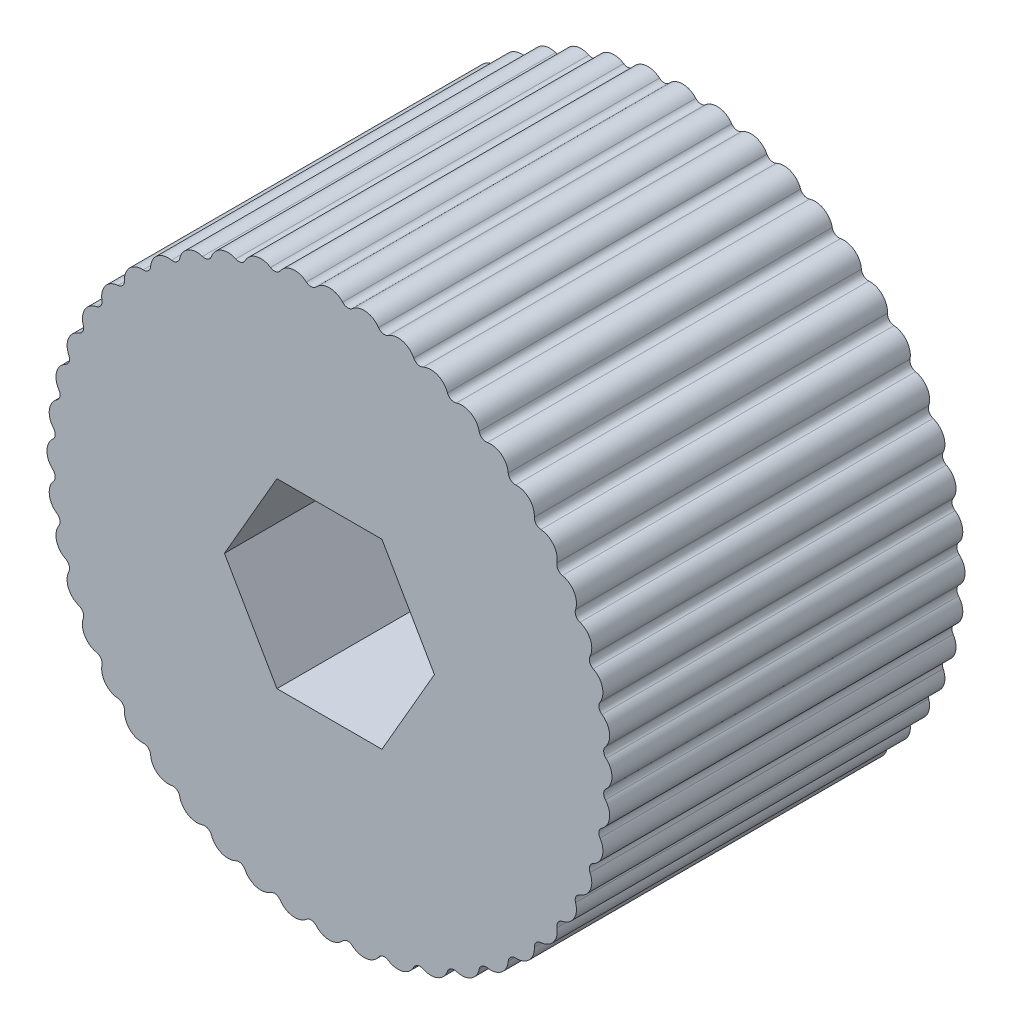
SolidWorks part; units mm, degrees
ref_plane "Front Plane" through (0, 0, 0) normal (0, 0, 1) x (1, 0, 0)
ref_plane "Top Plane" through (0, 0, 0) normal (0, 1, 0) x (1, 0, 0)
ref_plane "Right Plane" through (0, 0, 0) normal (1, 0, 0) x (0, 0, -1)
sketch "Sketch1" plane through (0, 0, 0) normal (0, 0, 1) x (1, 0, 0)
  line L1 (3.7762, 6.5405) -> (-3.7762, 6.5405)
  line L2 (-3.7762, 6.5405) -> (-7.5523, 0)
  line L3 (-7.5523, 0) -> (-3.7762, -6.5405)
  line L4 (-3.7762, -6.5405) -> (3.7762, -6.5405)
  line L5 (3.7762, -6.5405) -> (7.5523, 0)
  line L6 (7.5523, 0) -> (3.7762, 6.5405)
  circle A0 centre (0, 0) radius 6.5405 construction
  circle A1 centre (0, 0) radius 19.05
  dimension "D2" = 38.1
  dimension "D1" = 13.081
extrude "Boss-Extrude1" add sketch "Sketch1" along normal blind 25.4
sketch "Sketch2" plane through (0, 0, 25.4) normal (0, 0, 1) x (1, 0, 0)
  line L0 (19.0077, 1.2693) -> (19.0077, -1.2693)
  arc A0 (19.0077, 1.2693) -> (19.0077, -1.2693) centre (19.05, 0) cw
  circle A1 centre (0, 0) radius 19.05 construction
  dimension "D1" = 1.27
  dimension "D2" = 1.27
extrude "Boss-Extrude2" add sketch "Sketch2" against normal up to surface (25.4 mm away) up to face at (19.05, 0, 0)
pattern_circular "CirPattern1" count 48 over 360 about axis through (0, 0, 0) along (0, 0, 1) of "Boss-Extrude2"
fillet "Fillet1" radius 0.508 48 edges at (14.4769, -12.6959, 12.7) (12.6959, -14.4769, 12.7) (10.6977, -16.0102, 12.7) (8.5164, -17.2696, 12.7) (6.1894, -18.2334, 12.7) (3.7565, -18.8853, 12.7) (1.2594, -19.2141, 12.7) (-1.2594, -19.2141, 12.7) (-8.5164, -17.2696, 12.7) (-10.6977, -16.0102, 12.7) (-12.6959, -14.4769, 12.7) (-14.4769, -12.6959, 12.7) (-16.0102, -10.6977, 12.7) (-17.2696, -8.5164, 12.7) (-18.2334, -6.1894, 12.7) (-18.8853, -3.7565, 12.7) (-19.2141, -1.2594, 12.7) (-19.2141, 1.2594, 12.7) (-18.8853, 3.7565, 12.7) (-18.2334, 6.1894, 12.7) (-17.2696, 8.5164, 12.7) (-16.0102, 10.6977, 12.7) (-14.4769, 12.6959, 12.7) (-12.6959, 14.4769, 12.7) (-10.6977, 16.0102, 12.7) (-8.5164, 17.2696, 12.7) (-6.1894, 18.2334, 12.7) (-3.7565, 18.8853, 12.7) (-1.2594, 19.2141, 12.7) (1.2594, 19.2141, 12.7) (3.7565, 18.8853, 12.7) (6.1894, 18.2334, 12.7) (8.5164, 17.2696, 12.7) (10.6977, 16.0102, 12.7) (12.6959, 14.4769, 12.7) (14.4769, 12.6959, 12.7) (16.0102, 10.6977, 12.7) (17.2696, 8.5164, 12.7) (18.2334, 6.1894, 12.7) (18.8853, 3.7565, 12.7) (-3.7565, -18.8853, 12.7) (-6.1894, -18.2334, 12.7) (19.2141, 1.2594, 12.7) (19.2141, -1.2594, 12.7) (18.8853, -3.7565, 12.7) (18.2334, -6.1894, 12.7) (17.2696, -8.5164, 12.7) (16.0102, -10.6977, 12.7)
